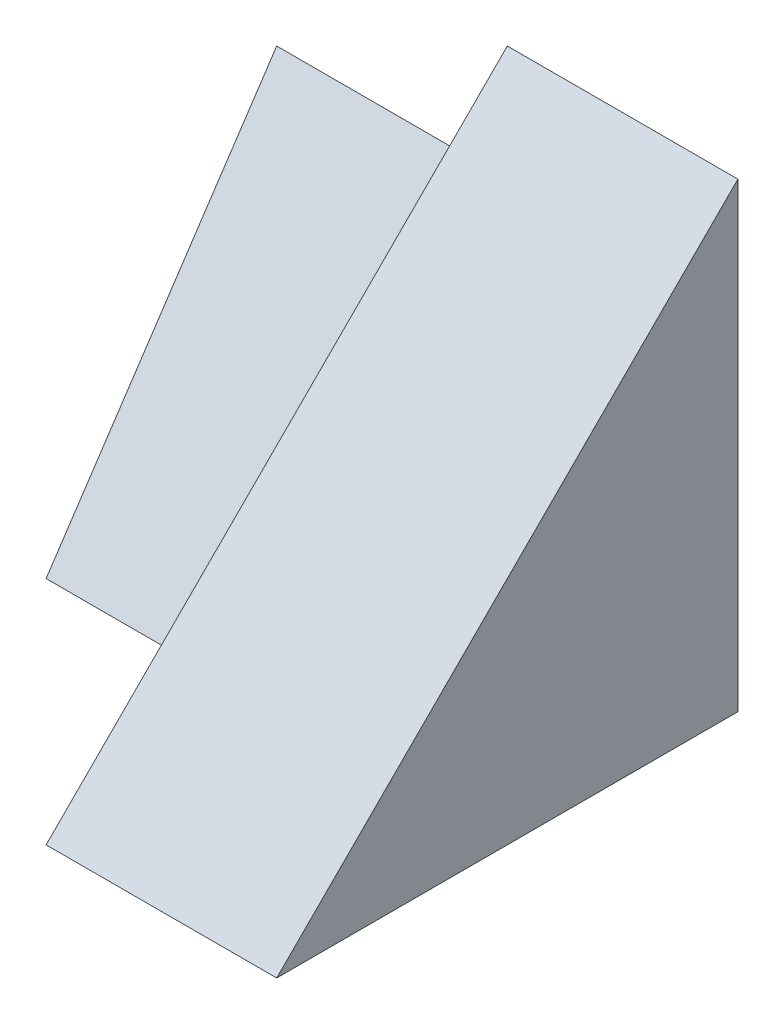
SolidWorks part; units mm, degrees
ref_plane "Front Plane" through (0, 0, 0) normal (0, 0, 1) x (1, 0, 0)
ref_plane "Top Plane" through (0, 0, 0) normal (0, 1, 0) x (1, 0, 0)
ref_plane "Right Plane" through (0, 0, 0) normal (1, 0, 0) x (0, 0, -1)
sketch "Sketch1" plane through (0, 0, 0) normal (1, 0, 0) x (0, 0, -1)
  line L1 (0, 0) -> (4, 0)
  line L2 (0, 0) -> (0, 4)
  line L3 (0, 4) -> (4, 4)
  line L4 (4, 0) -> (4, 4)
  dimension "D1" = 4
  dimension "D2" = 4
extrude "Boss-Extrude1" add sketch "Sketch1" along normal blind 2
sketch "Sketch2" plane through (0, 0, 0) normal (-1, 0, 0) x (0, 0, 1)
  line L1 (-4, 0) -> (-2, 0)
  line L2 (-4, 0) -> (-4, 3)
  line L3 (-4, 3) -> (-2, 3)
  line L4 (-2, 0) -> (-2, 3)
  dimension "D1" = 3
  dimension "D2" = 2
extrude "Boss-Extrude2" add sketch "Sketch2" along normal blind 2
sketch "Sketch3" plane through (-2, 0, 0) normal (-1, 0, 0) x (0, 0, 1)
  line L0 (-4, 3) -> (-2, 3)
  line L1 (-2, 3) -> (-2, 0)
  line L2 (-2, 0) -> (-4, 3)
extrude "Cut-Extrude1" cut sketch "Sketch3" against normal blind 2
sketch "Sketch4" plane through (2, 0, 0) normal (1, 0, 0) x (0, 0, -1)
  line L0 (4, 4) -> (0, 0)
  line L1 (0, 0) -> (0, 4)
  line L2 (0, 4) -> (4, 4)
extrude "Cut-Extrude2" cut sketch "Sketch4" against normal blind 2
